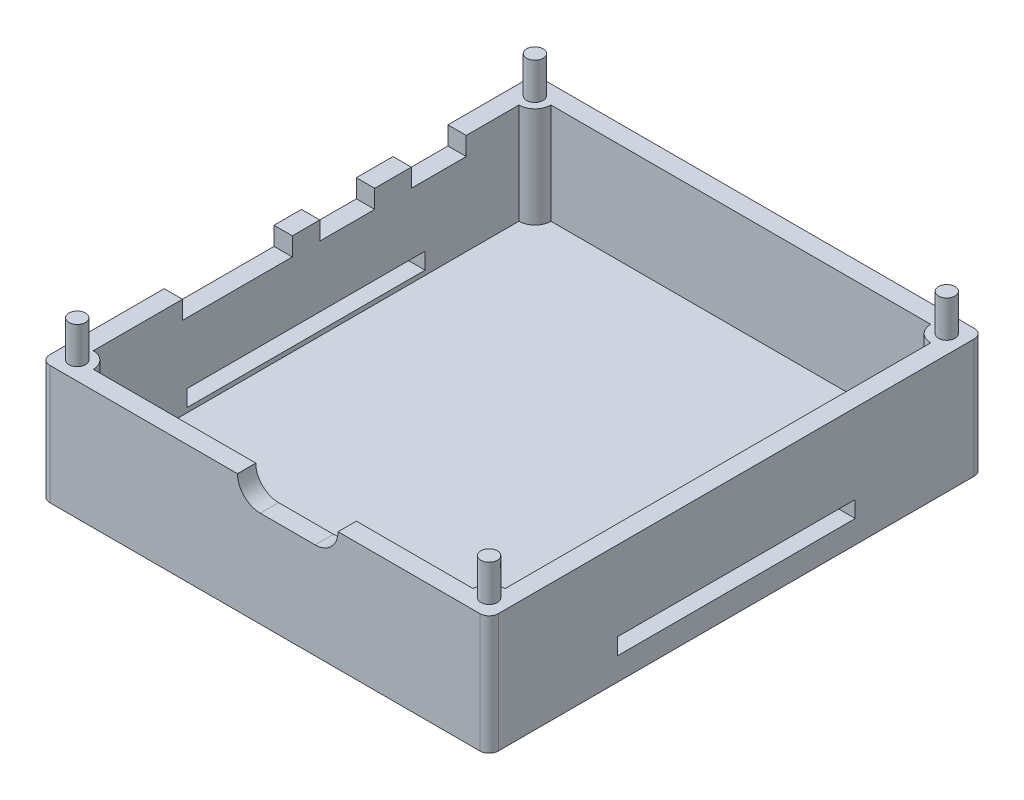
SolidWorks part; units mm, degrees
ref_plane "Front Plane" through (0, 0, 0) normal (0, 0, 1) x (1, 0, 0)
ref_plane "Top Plane" through (0, 0, 0) normal (0, 1, 0) x (1, 0, 0)
ref_plane "Right Plane" through (0, 0, 0) normal (1, 0, 0) x (0, 0, -1)
sketch "Sketch1" plane through (0, 0, 0) normal (0, 1, 0) x (1, 0, 0)
  line L1 (24.5, 27) -> (-24.5, 27)
  line L2 (24.5, 27) -> (24.5, -27)
  line L3 (24.5, -27) -> (-24.5, -27)
  line L4 (-24.5, 27) -> (-24.5, -27)
  line L5 (24.5, 27) -> (-24.5, -27) construction
  line L6 (24.5, -27) -> (-24.5, 27) construction
  point P0 (0, 0)
  dimension "D1" = 54
  dimension "D2" = 49
extrude "Boss-Extrude1" add sketch "Sketch1" along normal blind 2
sketch "Sketch2" plane through (0, 2, 0) normal (0, 1, 0) x (1, 0, 0)
  line L1 (24.5, 27) -> (-24.5, 27)
  line L2 (24.5, 27) -> (24.5, -27)
  line L3 (24.5, -27) -> (-24.5, -27)
  line L4 (-24.5, 27) -> (-24.5, -27)
  line L5 (24.5, 27) -> (-24.5, -27) construction
  line L6 (24.5, -27) -> (-24.5, 27) construction
  point P0 (0, 0)
extrude "Extrude-Thin1" add sketch "Sketch2" along normal blind 11 thin thin type one direction reverse wall 2
sketch "Sketch5" plane through (-24.5, 0, 0) normal (-1, 0, 0) x (0, 0, 1)
  line L0 (27, 13) -> (13.5, 13)
  line L1 (-27, 13) -> (27, 13) construction
  line L2 (13.5, 13) -> (1.5, 13)
  line L3 (1.5, 13) -> (-1.5, 13)
  line L4 (-1.5, 13) -> (-7.5, 13)
  line L5 (-7.5, 13) -> (-11.5, 13)
  line L6 (-11.5, 13) -> (-17.5, 13)
  dimension "D1" = 13.5
  dimension "D2" = 12
  dimension "D3" = 3
  dimension "D4" = 6
  dimension "D5" = 4
  dimension "D6" = 6
sketch "Sketch6" plane through (-24.5, 0, 0) normal (-1, 0, 0) x (0, 0, 1)
  line L0 (1.5, 13) -> (13.5, 13)
  line L1 (13.5, 13) -> (13.5, 11)
  line L2 (13.5, 11) -> (1.5, 11)
  line L3 (1.5, 11) -> (1.5, 13)
  dimension "D1" = 2
sketch "Sketch7" plane through (-24.5, 0, 0) normal (-1, 0, 0) x (0, 0, 1)
  line L0 (-1.5, 13) -> (-7.5, 13)
  line L1 (-7.5, 13) -> (-7.5, 11)
  line L2 (-7.5, 11) -> (-1.5, 11)
  line L3 (-1.5, 11) -> (-1.5, 13)
  line L4 (-11.5, 13) -> (-17.5, 13)
  line L5 (-17.5, 13) -> (-17.5, 11)
  line L6 (-17.5, 11) -> (-11.5, 11)
  line L7 (-11.5, 11) -> (-11.5, 13)
  dimension "D1" = 2
extrude "Cut-Extrude1" cut sketch "Sketch7" against normal blind 2
extrude "Cut-Extrude2" cut sketch "Sketch6" against normal blind 2
sketch "Sketch8" plane through (0, 0, 27) normal (0, 0, 1) x (1, 0, 0)
  line L0 (-24.5, 13) -> (-3, 13)
  line L1 (-24.5, 13) -> (24.5, 13) construction
  dimension "D1" = 21.5
sketch "Sketch9" plane through (0, 0, 27) normal (0, 0, 1) x (1, 0, 0)
  line L0 (-3, 13) -> (-0.5, 13)
  line L1 (-24.5, 13) -> (24.5, 13) construction
  line L2 (-0.5, 13) -> (5.5, 13)
  line L3 (5.5, 13) -> (8, 13)
  dimension "D1" = 2.5
  dimension "D2" = 6
  dimension "D3" = 2.5
sketch "Sketch11" plane through (0, 0, 27) normal (0, 0, 1) x (1, 0, 0)
  line L0 (-3, 13) -> (8, 13)
  line L1 (8, 13) -> (8, 11)
  line L2 (8, 11) -> (-3, 11)
  line L3 (-3, 11) -> (-3, 13)
  dimension "D1" = 2
sketch "Sketch14" plane through (0, 0, 27) normal (0, 0, 1) x (1, 0, 0)
  line L0 (-0.5, 13) -> (5.5, 13) construction
  line L1 (-0.5, 15.4932) -> (5.5, 15.4932)
  line L2 (-0.5, 10.5068) -> (5.5, 10.5068)
  arc A0 (-0.5, 15.4932) -> (-0.5, 10.5068) centre (-0.5, 13) ccw
  arc A1 (5.5, 10.5068) -> (5.5, 15.4932) centre (5.5, 13) ccw
  point P4 (2.5, 13)
extrude "Cut-Extrude3" cut sketch "Sketch14" against normal blind 2
sketch "Sketch15" plane through (0, 2, 0) normal (0, 1, 0) x (1, 0, 0)
  circle A0 centre (-22.5, -25) radius 1.75
  circle A1 centre (-22.5, 25) radius 1.75
  circle A2 centre (22.5, 25) radius 1.75
  circle A3 centre (22.5, -25) radius 1.75
sketch "Sketch17" plane through (0, 2, 0) normal (0, 1, 0) x (1, 0, 0)
  circle A0 centre (-22.5, -25) radius 0.9
  circle A1 centre (22.5, -25) radius 0.9
  circle A2 centre (22.5, 25) radius 0.9
  circle A3 centre (-22.5, 25) radius 0.9
extrude "Boss-Extrude2" add sketch "Sketch15" along normal blind 11 separate body
extrude "Boss-Extrude3" add sketch "Sketch17" along normal blind 15
sketch "Sketch20" plane through (-24.5, 0, 0) normal (-1, 0, 0) x (0, 0, 1)
  line L0 (0, 0) -> (0, 2.5) construction
  dimension "D1" = 2.5
sketch "Sketch21" plane through (-24.5, 0, 0) normal (-1, 0, 0) x (0, 0, 1)
  line L0 (0, 2.5) -> (-13, 2.5)
  line L1 (-13, 2.5) -> (-13, 4.3)
  line L2 (-13, 4.3) -> (13, 4.3)
  line L3 (13, 4.3) -> (13, 2.5)
  line L4 (13, 2.5) -> (0, 2.5)
  dimension "D1" = 13
  dimension "D2" = 13
  dimension "D3" = 1.8
extrude "Cut-Extrude4" cut sketch "Sketch21" against normal blind 49
fillet "Fillet1" radius 1 4 edges at (-24.5, 6.5, -27) (24.5, 6.5, -27) (24.5, 6.5, 27) (-24.5, 6.5, 27)
